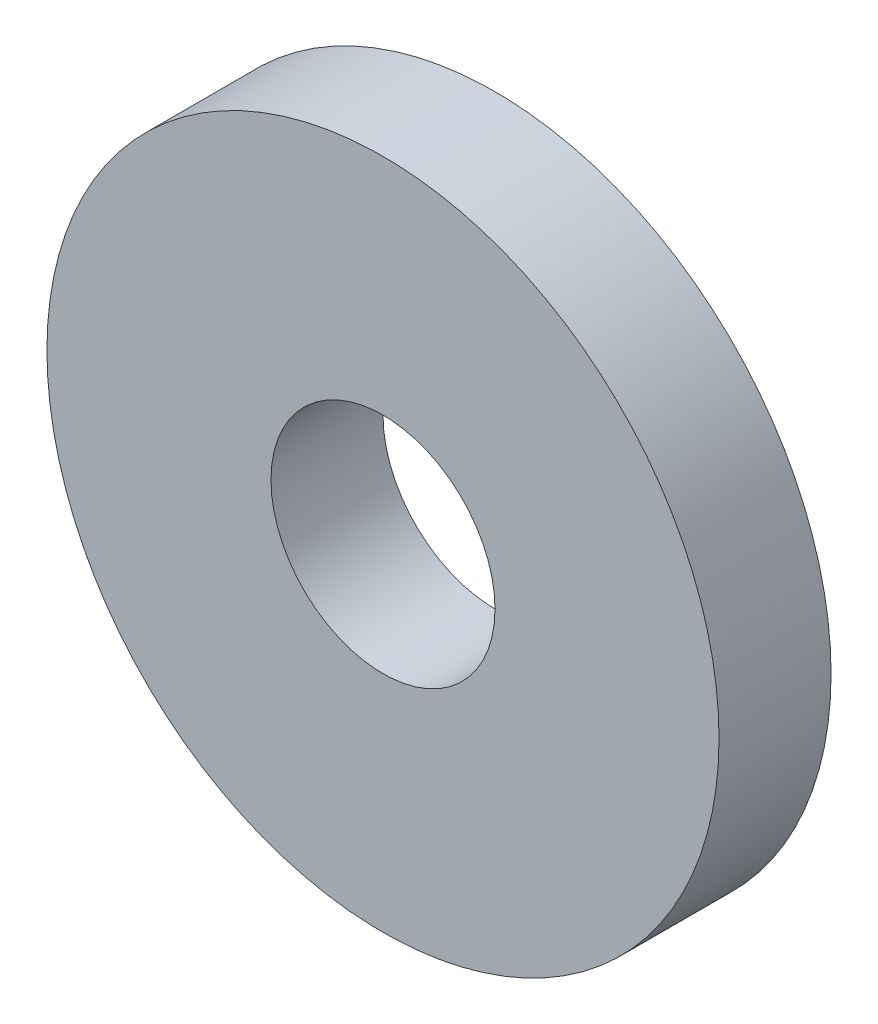
SolidWorks part; units mm, degrees
ref_plane "Front Plane" through (0, 0, 0) normal (0, 0, 1) x (1, 0, 0)
ref_plane "Top Plane" through (0, 0, 0) normal (0, 1, 0) x (1, 0, 0)
ref_plane "Right Plane" through (0, 0, 0) normal (1, 0, 0) x (0, 0, -1)
sketch "Sketch1" plane through (0, 0, 0) normal (0, 0, 1) x (1, 0, 0)
  circle A0 centre (0, 0) radius 15
  circle A1 centre (0, 0) radius 5
extrude "Boss-Extrude1" add sketch "Sketch1" along normal blind 5
